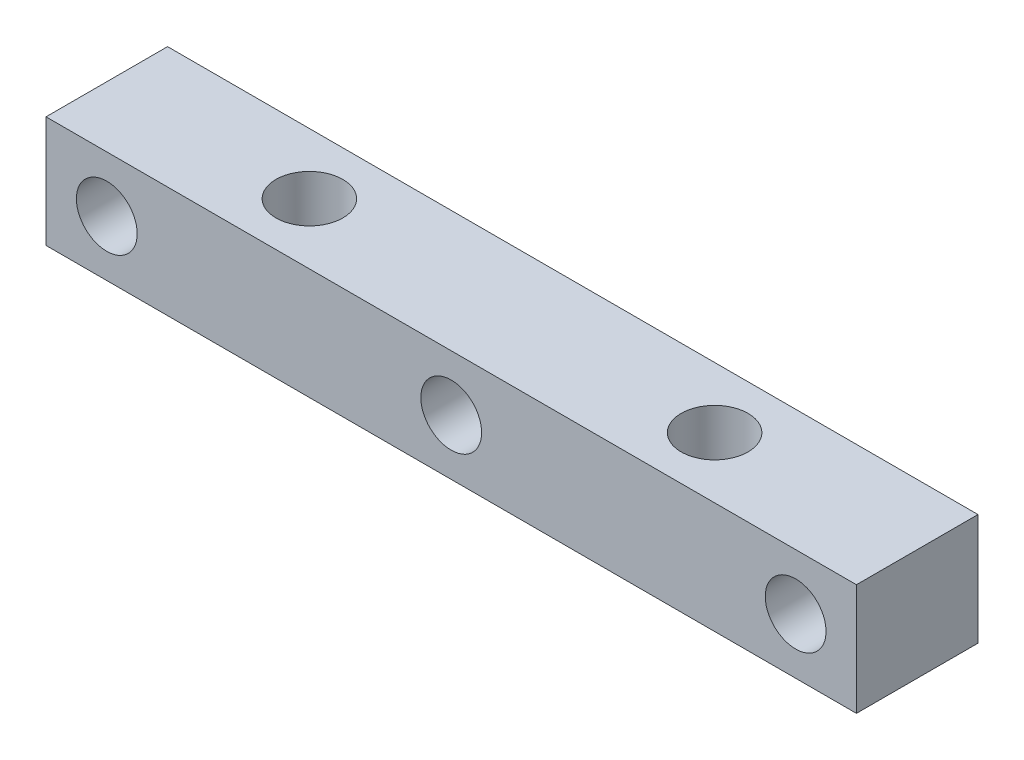
SolidWorks part; units mm, degrees
ref_plane "Front" through (0, 0, 0) normal (0, 0, 1) x (1, 0, 0)
ref_plane "Top" through (0, 0, 0) normal (0, 1, 0) x (1, 0, 0)
ref_plane "Right" through (0, 0, 0) normal (1, 0, 0) x (0, 0, -1)
sketch "Esquisse1" plane through (0, 0, 0) normal (0, 0, 1) x (1, 0, 0)
  line L1 (0, 0) -> (40, 0)
  line L2 (0, 0) -> (0, 5.5)
  line L3 (0, 5.5) -> (40, 5.5)
  line L4 (40, 0) -> (40, 5.5)
  dimension "D1" = 5.5
  dimension "D2" = 40
extrude "Boss.-Extru.1" add sketch "Esquisse1" along normal blind 6
sketch "Esquisse2" plane through (0, 0, 6) normal (0, 0, 1) x (1, 0, 0)
  line L0 (0, 2.75) -> (20, 2.75) construction
  line L1 (0, 5.5) -> (0, 0) construction
  line L2 (20, 2.75) -> (20, 5.5) construction
  line L3 (40, 5.5) -> (0, 5.5) construction
  circle A0 centre (20, 2.75) radius 1.5
  circle A1 centre (3, 2.75) radius 1.5
  circle A2 centre (37, 2.75) radius 1.5
  dimension "D1" = 3
  dimension "D2" = 17
extrude "Enlèv. mat.-Extru.1" cut sketch "Esquisse2" against normal through all both and the other way through all
sketch "Esquisse3" plane through (0, 5.5, 0) normal (0, 1, 0) x (1, 0, 0)
  line L0 (40, -3) -> (0, -3) construction
  line L1 (40, -6) -> (40, 0) construction
  line L2 (0, -6) -> (0, 0) construction
  line L3 (20, -3) -> (20, 0) construction
  line L4 (40, 0) -> (0, 0) construction
  circle A0 centre (10, -3) radius 1.65
  circle A1 centre (30, -3) radius 1.65
  dimension "D1" = 3.3
  dimension "D2" = 20
extrude "Enlèv. mat.-Extru.2" cut sketch "Esquisse3" against normal through all both and the other way through all
